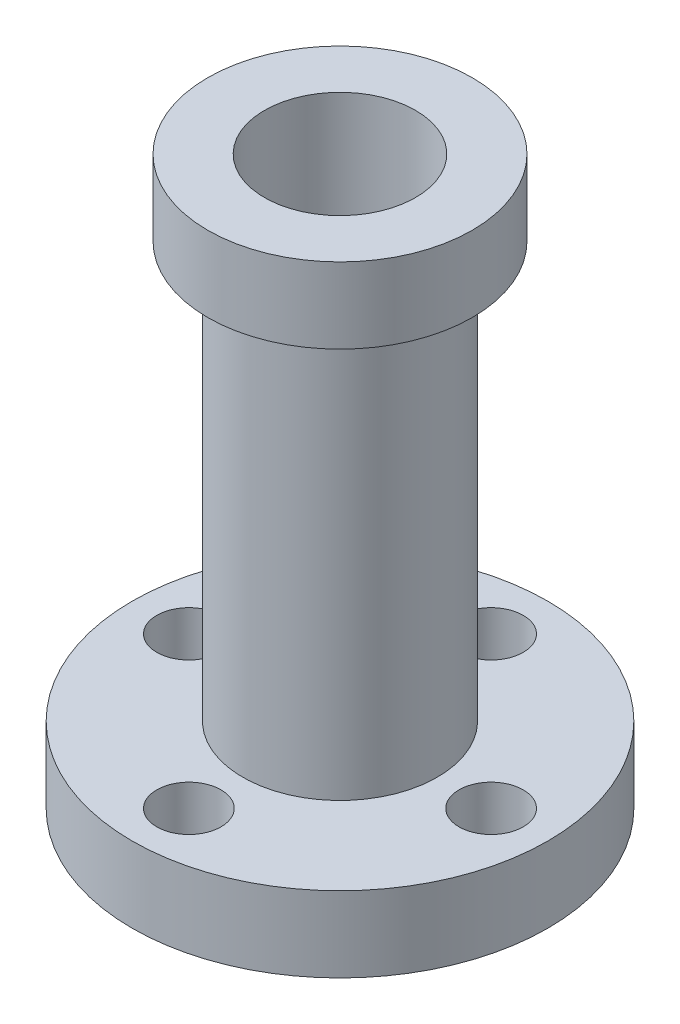
SolidWorks part; units mm, degrees
ref_plane "Front" through (0, 0, 0) normal (0, 0, 1) x (1, 0, 0)
ref_plane "Top" through (0, 0, 0) normal (0, 1, 0) x (1, 0, 0)
ref_plane "Right" through (0, 0, 0) normal (1, 0, 0) x (0, 0, -1)
sketch "Sketch2" plane through (0, 0, 0) normal (0, 0, 1) x (1, 0, 0)
  line L0 (0, 0) -> (0, 30) construction
  line L1 (4, 30) -> (4, 0)
  line L2 (4, 0) -> (11, 0)
  line L3 (11, 0) -> (11, 4)
  line L4 (11, 4) -> (5.15, 4)
  line L6 (7, 30) -> (4, 30)
  line L7 (0, 30) -> (4, 30) construction
  line L8 (5.15, 4) -> (5.15, 26)
  line L9 (5.15, 26) -> (7, 26)
  line L10 (7, 26) -> (7, 30)
  dimension "D1" = 30
  dimension "D2" = 4
  dimension "D3" = 22
  dimension "D4" = 4
  dimension "D5" = 8
  dimension "D6" = 10.3
  dimension "D7" = 14
revolve "Revolve1" add sketch "Sketch2" angle 360 about L0
hole_wizard "M3 Clearance Hole1" positions "Sketch3" profile "Sketch4" hole size "M3" standard "ANSI Metric"
sketch "Sketch3" plane through (0, 0, 0) normal (0, -1, 0) x (-1, 0, 0)
  line L0 (0, -8) -> (0, 0) construction
  line L1 (0, 0) -> (-8, 0) construction
  line L4 (0, 8) -> (0, 0) construction
  line L7 (8, 0) -> (0, 0) construction
  line L8 (-8, 0) -> (-11, 0) construction
  circle A0 centre (0, 0) radius 11 construction
  point P0 (0, -8)
  point P2 (-8, 0)
  point P4 (0, 8)
  point P6 (8, 0)
  dimension "D1" = 8
  dimension "D2" = 3
sketch "Sketch4" plane through (0, 0, 8) normal (1, 0, 0) x (0, 0, -1)
  line L0 (0, 0) -> (0, 5.0205)
  line L1 (0, 5.0205) -> (1.7, 3.999)
  line L2 (1.7, 3.999) -> (1.7, 0)
  line L5 (1.7, 0) -> (0, 0)
  line L10 (0, 5.0205) -> (-1.7, 3.999) construction
  line L11 (0, -6.35) -> (0, 107.95) construction
  dimension "Hole Dia." = 3.4
  dimension "Hole Depth" = 3.999
  dimension "Drill Angle" = 118
sketch "Sketch5" [suppressed] plane through (0, 0, 0) normal (0, -1, 0) x (1, 0, 0)
  line L0 (0, 0) -> (-10.3534, 0) construction
  line L1 (-14.4068, -16.6856) -> (-6.3, -16.6856)
  line L2 (-14.4068, -16.6856) -> (-14.4068, 16.6856)
  line L3 (-14.4068, 16.6856) -> (-6.3, 16.6856)
  line L4 (-6.3, -16.6856) -> (-6.3, 16.6856)
  line L5 (-14.4068, -16.6856) -> (-6.3, 16.6856) construction
  line L6 (-14.4068, 16.6856) -> (-6.3, -16.6856) construction
  line L7 (0, 0) -> (0, 18.4736) construction
  line L8 (14.4068, 16.6856) -> (6.3, -16.6856) construction
  line L9 (14.4068, -16.6856) -> (6.3, 16.6856) construction
  line L10 (6.3, -16.6856) -> (6.3, 16.6856)
  line L11 (14.4068, 16.6856) -> (6.3, 16.6856)
  line L12 (14.4068, -16.6856) -> (14.4068, 16.6856)
  line L13 (14.4068, -16.6856) -> (6.3, -16.6856)
  point P0 (-10.3534, 0)
  point P13 (10.3534, 0)
  dimension "D1" = 6.3
extrude "Cut-Extrude1" [suppressed] cut sketch "Sketch5" against normal up to surface (4 mm away)
hole_wizard "M3x0.5 Tapped Hole1" [suppressed] positions "Sketch7" profile "Sketch9" tap size "M3x0.5" standard "ANSI Metric"
sketch "Sketch7" plane through (0, 0, 0) normal (0, -1, 0) x (-1, 0, 0)
  line L0 (0, 9) -> (0, 0) construction
  line L1 (0, 0) -> (0, -9) construction
  point P0 (0, 9)
  point P2 (0, -9)
  dimension "D1" = 9
sketch "Sketch9" plane through (0, 0, -9) normal (1, 0, 0) x (0, 0, -1)
  line L0 (0, 0) -> (0, 30)
  line L1 (0, 30) -> (1.25, 30)
  line L2 (1.25, 30) -> (1.25, 0)
  line L5 (1.25, 0) -> (0, 0)
  line L11 (0, -6.35) -> (0, 107.95) construction
  dimension "Thru Tap Drill Dia." = 2.5
  dimension "Thru Tap Drill Depth" = 30
cosmetic thread "Hole Thread1" [suppressed] parameters "D2"=3
cosmetic thread "Hole Thread2" [suppressed] parameters "D2"=3
